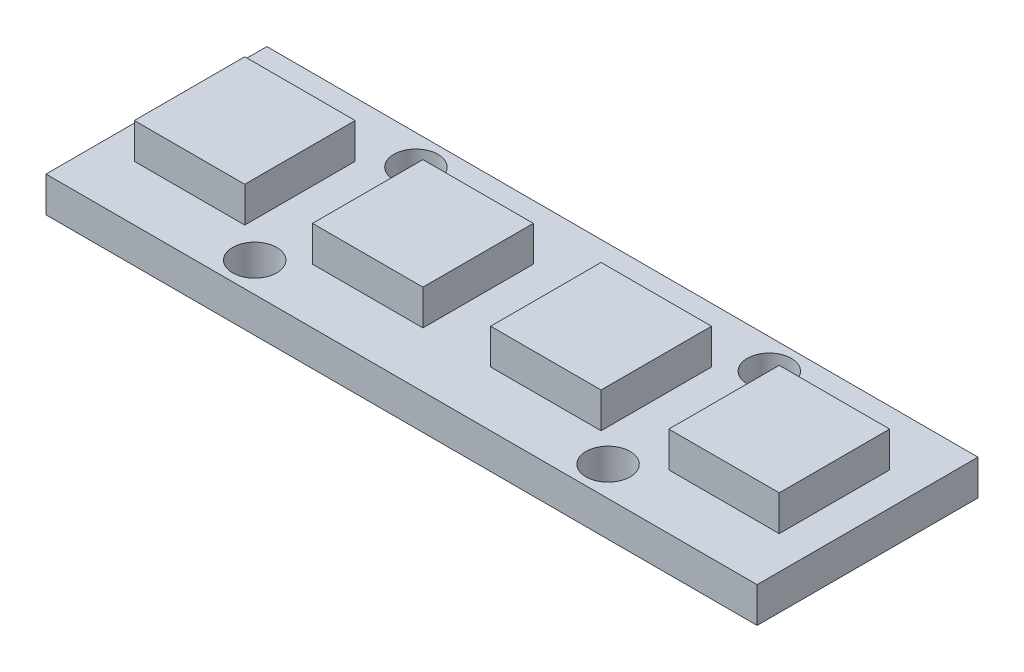
SolidWorks part; units mm, degrees
ref_plane "Front Plane" through (0, 0, 0) normal (0, 0, 1) x (1, 0, 0)
ref_plane "Top Plane" through (0, 0, 0) normal (0, 1, 0) x (1, 0, 0)
ref_plane "Right Plane" through (0, 0, 0) normal (1, 0, 0) x (0, 0, -1)
sketch "Sketch1" plane through (0, 0, 0) normal (0, 1, 0) x (1, 0, 0)
  line L0 (-16.1, 0) -> (16.1, 0) construction
  line L1 (-16.1, 5) -> (16.1, 5)
  line L2 (-16.1, 5) -> (-16.1, -5)
  line L3 (-16.1, -5) -> (16.1, -5)
  line L4 (16.1, 5) -> (16.1, -5)
  line L5 (-16.1, 5) -> (16.1, -5) construction
  line L6 (-16.1, -5) -> (16.1, 5) construction
  line L7 (-16.1, 3.65) -> (16.1, 3.65) construction
  line L8 (0, 5) -> (0, -5) construction
  circle A0 centre (-8, 3.65) radius 1
  circle A1 centre (8, 3.65) radius 1
  circle A2 centre (8, -3.65) radius 1
  circle A3 centre (-8, -3.65) radius 1
  point P0 (0, 0)
  dimension "D3" = 2
  dimension "D1" = 32.2
  dimension "D2" = 10
  dimension "D4" = 7.3
  dimension "D5" = 16
extrude "PCB" add sketch "Sketch1" along normal blind 1.6
sketch "Sketch2" plane through (0, 1.6, 0) normal (0, 1, 0) x (1, 0, 0)
  line L0 (-16.1, 0) -> (16.1, 0) construction
  line L1 (-16.1, 5) -> (-16.1, -5) construction
  line L2 (16.1, -5) -> (16.1, 5) construction
  line L3 (0, 5) -> (0, -5) construction
  line L4 (-14.6, 2.5) -> (-9.6, 2.5)
  line L5 (-14.6, 2.5) -> (-14.6, -2.5)
  line L6 (-14.6, -2.5) -> (-9.6, -2.5)
  line L7 (-9.6, 2.5) -> (-9.6, -2.5)
  line L8 (-14.6, 2.5) -> (-9.6, -2.5) construction
  line L9 (-14.6, -2.5) -> (-9.6, 2.5) construction
  line L10 (16.1, 5) -> (-16.1, 5) construction
  line L11 (-16.1, -5) -> (16.1, -5) construction
  line L12 (-6.5333, -2.5) -> (-1.5333, -2.5)
  line L13 (-1.5333, 2.5) -> (-1.5333, -2.5)
  line L14 (-6.5333, 2.5) -> (-1.5333, 2.5)
  line L15 (-6.5333, 2.5) -> (-6.5333, -2.5)
  line L16 (1.5333, -2.5) -> (6.5333, -2.5)
  line L17 (6.5333, 2.5) -> (6.5333, -2.5)
  line L18 (1.5333, 2.5) -> (6.5333, 2.5)
  line L19 (1.5333, 2.5) -> (1.5333, -2.5)
  line L20 (9.6, -2.5) -> (14.6, -2.5)
  line L21 (14.6, 2.5) -> (14.6, -2.5)
  line L22 (9.6, 2.5) -> (14.6, 2.5)
  line L23 (9.6, 2.5) -> (9.6, -2.5)
  line L24 (-14.6, 2.5) -> (-16.1, 2.5) construction
  line L25 (14.6, 2.5) -> (16.1, 2.5) construction
  point P6 (-12.1, 0)
  dimension "D1" = 5
  dimension "D2" = 1.5
  dimension "D3" = 4
extrude "Boss-Extrude2" add sketch "Sketch2" along normal blind 1.6
